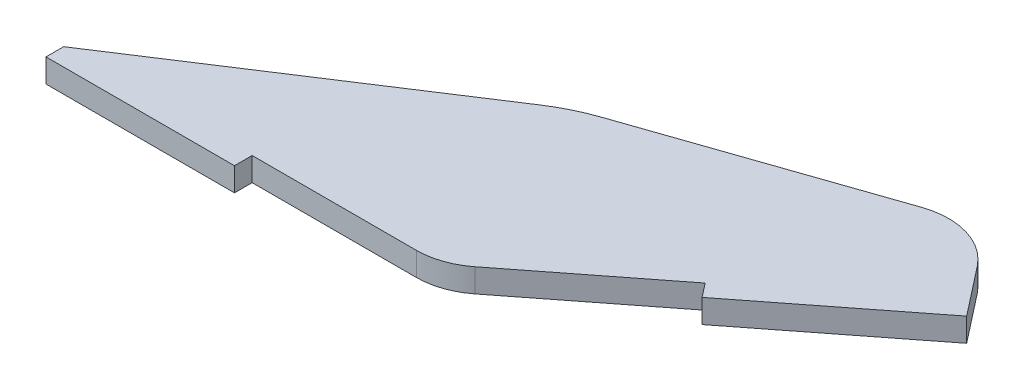
SolidWorks part; units mm, degrees
material "Plain Carbon Steel"
ref_plane "Front Plane" through (0, 0, 0) normal (0, 0, 1) x (1, 0, 0)
ref_plane "Top Plane" through (0, 0, 0) normal (0, 1, 0) x (1, 0, 0)
ref_plane "Right Plane" through (0, 0, 0) normal (1, 0, 0) x (0, 0, -1)
sketch "Sketch1" plane through (0, 0, 0) normal (0, 1, 0) x (1, 0, 0)
  line L0 (-50.8, 0) -> (0, 0)
  line L1 (0, 0) -> (40.0309, 31.2756)
  line L2 (-50.8, 0) -> (-50.8, 12.7)
  line L3 (-50.8, 12.7) -> (32.212, 41.2833)
  line L4 (32.212, 41.2833) -> (40.0309, 31.2756)
  dimension "D1" = 50.8
  dimension "D2" = 50.8
  dimension "D3" = 38
  dimension "D4" = 12.7
extrude "Boss-Extrude1" add sketch "Sketch1" along normal blind 3.175
sketch "Sketch2" plane through (0, 3.175, 0) normal (0, 1, 0) x (1, 0, 0)
  line L0 (20.0155, 15.6378) -> (40.0309, 31.2756)
  line L1 (-50.8, 0) -> (-25.4, 0)
  line L2 (-50.8, 0) -> (-50.8, -2.3813)
  line L3 (-50.8, -2.3813) -> (-25.4, -2.3813)
  line L4 (-25.4, 0) -> (-25.4, -2.3813)
  line L5 (0, 0) -> (40.0309, 31.2756) construction
  line L6 (40.0309, 31.2756) -> (41.497, 29.3992)
  line L7 (41.497, 29.3992) -> (21.4815, 13.7614)
  line L8 (21.4815, 13.7614) -> (20.0155, 15.6378)
  dimension "D1" = 2.3813
extrude "Boss-Extrude2" add sketch "Sketch2" against normal up to surface (3.175 mm away) up to face at (-5.8714, 0, -17.0518)
fillet "Fillet1" radius 9.525 3 edges at (-50.8, 1.5875, -12.7) (32.212, 1.5875, -41.2833) (0, 1.5875, 0)
sketch "Sketch3" plane through (0, 3.175, 0) normal (0, 1, 0) x (1, 0, 0)
  line L0 (-50.8, 0) -> (-9.294, 26.9917)
  line L1 (-50.8, 5.9059) -> (-50.8, -2.3813) construction
  line L2 (-231.775, 0) -> (-1.5875, 0) construction
  line L3 (25.7881, 39.0714) -> (-44.376, 14.9119) construction
  line L4 (-9.294, 26.9917) -> (-44.376, 14.9119)
  line L5 (-50.8, 5.9059) -> (-50.8, 0)
  arc A0 (-50.8, 5.9059) -> (-44.376, 14.9119) centre (-41.275, 5.9059) cw
extrude "Cut-Extrude1" cut sketch "Sketch3" against normal through all
fillet "Fillet2" radius 25.4 1 edges
